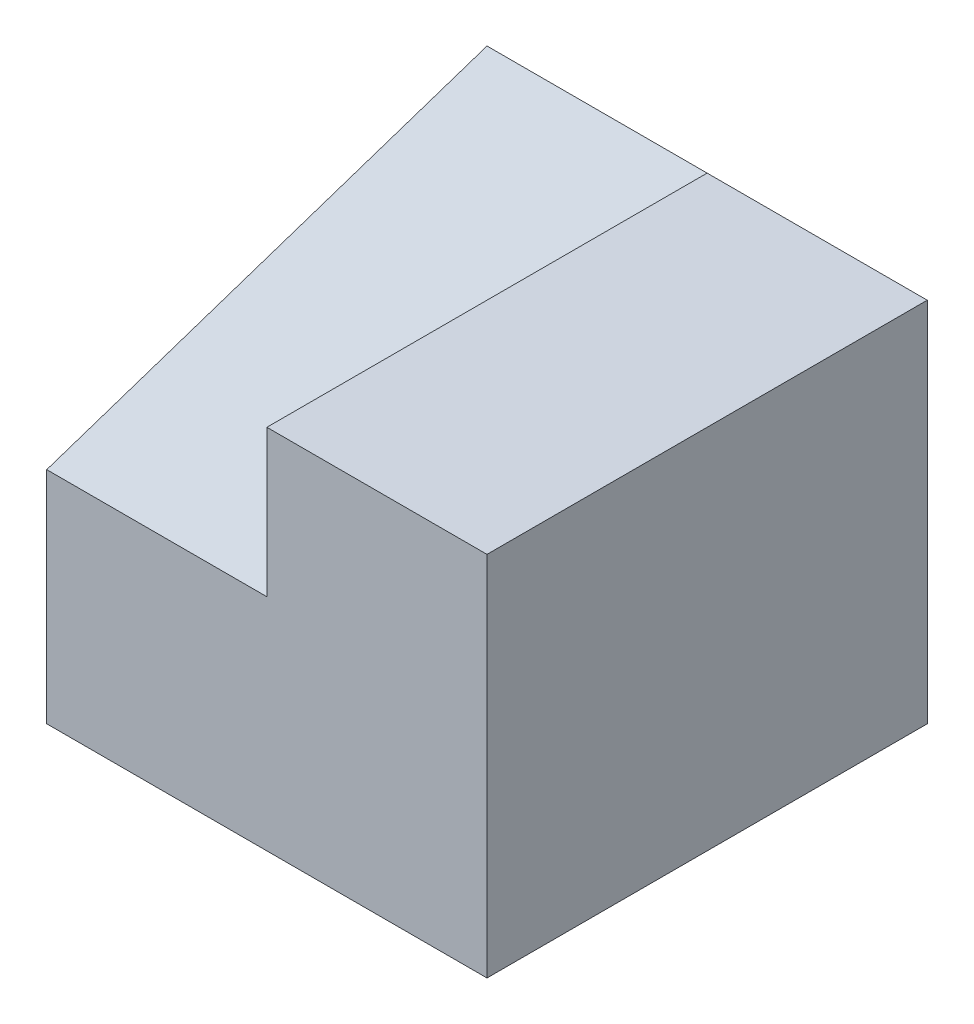
SolidWorks part; units mm, degrees
ref_plane "Front Plane" through (0, 0, 0) normal (0, 0, 1) x (1, 0, 0)
ref_plane "Top Plane" through (0, 0, 0) normal (0, 1, 0) x (1, 0, 0)
ref_plane "Right Plane" through (0, 0, 0) normal (1, 0, 0) x (0, 0, -1)
sketch "Sketch3" plane through (0, 0, 0) normal (0, 0, 1) x (1, 0, 0)
  line L1 (0, 0) -> (6, 0)
  line L2 (0, 0) -> (0, 5)
  line L3 (0, 5) -> (6, 5)
  line L4 (6, 0) -> (6, 5)
  dimension "D1" = 5
  dimension "D2" = 6
extrude "Boss-Extrude6" add sketch "Sketch3" along normal blind 6
sketch "Sketch7" plane through (0, 0, 0) normal (-1, 0, 0) x (0, 0, 1)
  line L0 (0, 5) -> (6, 3)
  line L1 (6, 5) -> (6, 0) construction
  line L2 (6, 3) -> (6, 5)
  line L3 (6, 5) -> (0, 5)
  dimension "D1" = 2
extrude "Cut-Extrude3" cut sketch "Sketch7" against normal blind 3
